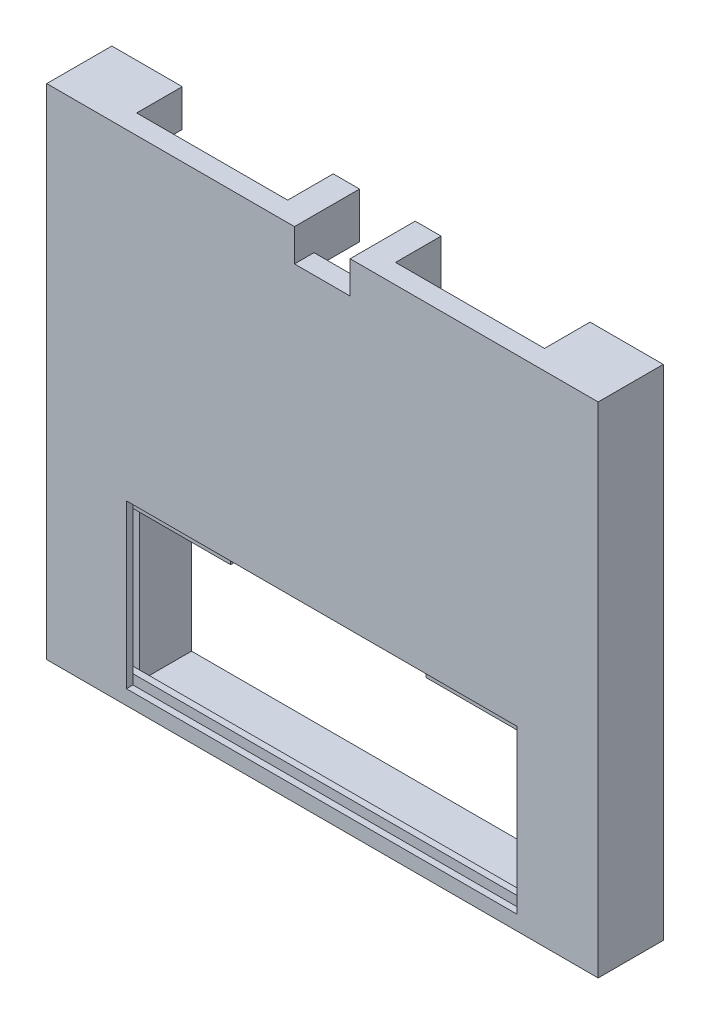
SolidWorks part; units mm, degrees
ref_plane "Front Plane" through (0, 0, 0) normal (0, 0, 1) x (1, 0, 0)
ref_plane "Top Plane" through (0, 0, 0) normal (0, 1, 0) x (1, 0, 0)
ref_plane "Right Plane" through (0, 0, 0) normal (1, 0, 0) x (0, 0, -1)
sketch "Sketch1" plane through (0, 0, 0) normal (0, 0, 1) x (1, 0, 0)
  line L5 (-29.5833, 179.7818) -> (185.5833, 179.7818)
  line L6 (-29.5833, 179.7818) -> (-29.5833, -14.8849)
  line L7 (-29.5833, -14.8849) -> (185.5833, -14.8849)
  line L8 (185.5833, 179.7818) -> (185.5833, -14.8849)
extrude "Boss-Extrude1" add sketch "Sketch1" along normal blind 25.4
sketch "Sketch2" plane through (0, 0, 0) normal (0, 0, -1) x (-1, 0, 0)
  line L0 (-185.5833, 179.7818) -> (29.5833, 179.7818) construction
  line L3 (2.1146, 179.7818) -> (-157.0228, 179.7818)
  line L17 (-148.7667, 67.5719) -> (-91.8301, 67.5719)
  line L19 (-91.8301, 67.5719) -> (-91.8301, 31.6046)
  line L20 (-91.8301, 31.6046) -> (-66.1599, 31.6046)
  line L21 (-66.1599, 67.5719) -> (-66.1599, 31.6046)
  line L22 (-66.1599, 67.5719) -> (-7.2333, 67.388)
  line L23 (-157.0228, 164.2008) -> (-157.0228, 179.7818)
  line L24 (-157.0228, 164.2008) -> (-171.7655, 164.2008)
  line L26 (-148.7667, 67.5719) -> (-171.7655, 67.5719)
  line L27 (-171.7655, 164.2008) -> (-171.7655, 67.5719)
  line L28 (-7.2333, 67.388) -> (16.5817, 67.388)
  line L30 (2.1146, 165.2927) -> (16.5817, 165.2927)
  line L31 (16.5817, 67.388) -> (16.5817, 165.2927)
  line L32 (2.1146, 165.2927) -> (2.1146, 179.7818)
  circle A0 centre (5.4167, 47.0318) radius 5.08
  circle A3 centre (-161.4167, 47.0318) radius 5.08
  point P6 (2.1146, 163.9279)
  point P7 (16.5817, 165.2927)
  point P18 (0, 0)
  point P19 (-157.0228, 164.2008)
sketch "Sketch3" plane through (0, 0, 0) normal (0, 0, -1) x (-1, 0, 0)
  line L9 (-153.9148, 54.3331) -> (-1.5148, 54.3331)
  line L10 (-153.9148, 54.3331) -> (-153.9148, -9.1669)
  line L11 (-153.9148, -9.1669) -> (-1.5148, -9.1669)
  line L12 (-1.5148, 54.3331) -> (-1.5148, -9.1669)
  point P7 (-153.9148, 54.3331)
  point P8 (-1.5148, -9.1669)
sketch "Sketch4" plane through (0, 0, 0) normal (0, 0, -1) x (-1, 0, 0)
  line L0 (2.1146, 179.7818) -> (-157.0228, 179.7818) construction
  line L1 (-67.0744, 167.1688) -> (-88.7926, 167.1688)
  line L2 (-67.0744, 167.1688) -> (-67.0744, 179.7818)
  line L3 (-67.0744, 179.7818) -> (-88.7926, 179.7818)
  line L4 (-88.7926, 167.1688) -> (-88.7926, 179.7818)
extrude "Cut-Extrude1" cut sketch "Sketch2" against normal blind 17.78
extrude "Cut-Extrude2" cut sketch "Sketch3" against normal through all
extrude "Cut-Extrude3" cut sketch "Sketch4" against normal through all
ref_plane "Plane1" through (-0.3333, 220.6137, 13) normal (1, 0, 0) x (0, 0, -1)
sketch "Sketch6" plane through (0, 54.3331, 0) normal (0, -1, 0) x (1, 0, 0)
  line L0 (1.5148, 25.4) -> (1.5148, 0) construction
  line L1 (1.5148, 22.86) -> (39.6148, 22.86)
  line L2 (1.5148, 22.86) -> (1.5148, 20.32)
  line L3 (1.5148, 20.32) -> (39.6148, 20.32)
  line L4 (39.6148, 22.86) -> (39.6148, 20.32)
  line L6 (153.9148, 25.4) -> (153.9148, 0) construction
  line L7 (153.9148, 22.86) -> (115.8399, 22.86)
  line L8 (153.9148, 22.86) -> (153.9148, 20.32)
  line L9 (153.9148, 20.32) -> (115.8399, 20.32)
  line L10 (115.8399, 22.86) -> (115.8399, 20.32)
  line L12 (91.8301, 0) -> (153.9148, 0) construction
  line L13 (1.5148, 0) -> (66.1599, 0) construction
  dimension "D1" = 2.54
  dimension "D2" = 20.32
  dimension "D3" = 38.1
  dimension "D4" = 20.32
extrude "Boss-Extrude2" add sketch "Sketch6" along normal blind 3.81
sketch "Sketch8" plane through (0, -9.1669, 0) normal (0, 1, 0) x (1, 0, 0)
  line L0 (153.9148, -25.4) -> (153.9148, 0) construction
  line L1 (153.9148, -22.86) -> (1.5148, -22.86)
  line L2 (153.9148, -22.86) -> (153.9148, -20.32)
  line L3 (153.9148, -20.32) -> (1.5148, -20.32)
  line L4 (1.5148, -22.86) -> (1.5148, -20.32)
  line L6 (1.5148, -25.4) -> (1.5148, 0) construction
  line L7 (153.9148, 0) -> (1.5148, 0) construction
  point P8 (1.5148, -15.5181)
  dimension "D1" = 2.54
  dimension "D2" = 20.32
extrude "Boss-Extrude3" add sketch "Sketch8" along normal blind 3.81
sketch "Sketch9" plane through (1.5148, 0, 0) normal (1, 0, 0) x (0, 0, -1)
  line L6 (-22.86, -5.3569) -> (-20.32, -5.3569)
  line L7 (-22.86, -5.3569) -> (-22.86, 50.5231)
  line L8 (-22.86, 50.5231) -> (-20.32, 50.5231)
  line L9 (-20.32, -5.3569) -> (-20.32, 50.5231)
extrude "Cut-Extrude8" cut sketch "Sketch9" against normal blind 3.81
sketch "Sketch10" plane through (0, 0, 17.78) normal (0, 0, -1) x (-1, 0, 0)
  line L1 (-88.7926, 179.7818) -> (-98.895, 179.7818)
  line L2 (-88.7926, 179.7818) -> (-88.7926, 161.9227)
  line L3 (-88.7926, 161.9227) -> (-98.895, 161.9227)
  line L4 (-98.895, 179.7818) -> (-98.895, 161.9227)
  line L5 (-67.0744, 179.7818) -> (-56.8125, 179.7818)
  line L6 (-67.0744, 179.7818) -> (-67.0744, 161.9227)
  line L7 (-67.0744, 161.9227) -> (-56.8125, 161.9227)
  line L8 (-56.8125, 179.7818) -> (-56.8125, 161.9227)
extrude "Boss-Extrude4" add sketch "Sketch10" along normal blind 17.78
